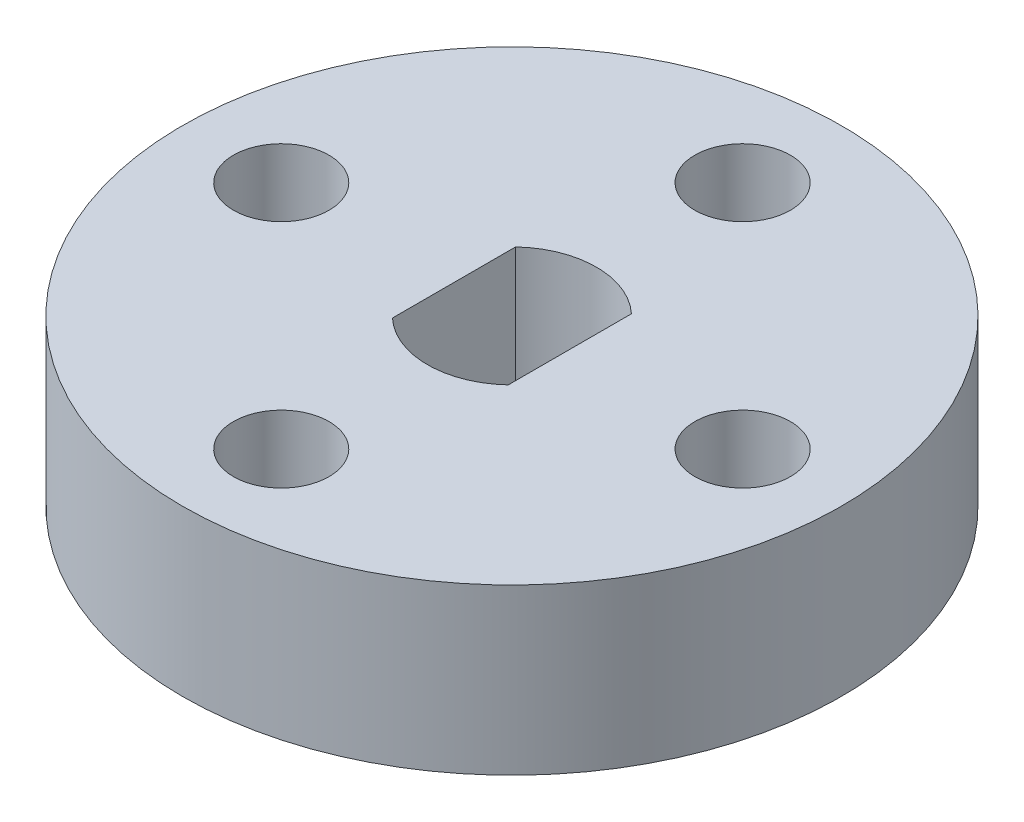
SolidWorks part; units mm, degrees
ref_plane "前视基准面" through (0, 0, 0) normal (0, 0, 1) x (1, 0, 0)
ref_plane "上视基准面" through (0, 0, 0) normal (0, 1, 0) x (1, 0, 0)
ref_plane "右视基准面" through (0, 0, 0) normal (1, 0, 0) x (0, 0, -1)
sketch "草图1" plane through (0, 0, 0) normal (0, 1, 0) x (1, 0, 0)
  line L0 (1.7575, 0) -> (1.7575, 1.8683)
  line L1 (1.7575, 0) -> (1.7575, -1.8683)
  line L2 (-1.7575, 0) -> (-1.7575, 1.8683)
  line L3 (-1.7575, 0) -> (-1.7575, -1.8683)
  circle A0 centre (0, 0) radius 10
  arc A1 (1.7575, 1.8683) -> (-1.7575, 1.8683) centre (0, 0) ccw
  arc A2 (-1.7575, -1.8683) -> (1.7575, -1.8683) centre (0, 0) ccw
  circle A3 centre (7, 0) radius 1.45
  circle A4 centre (0, 7) radius 1.45
  circle A5 centre (-7, 0) radius 1.45
  circle A6 centre (0, -7) radius 1.45
extrude "凸台-拉伸1" add sketch "草图1" along normal mid plane 5
